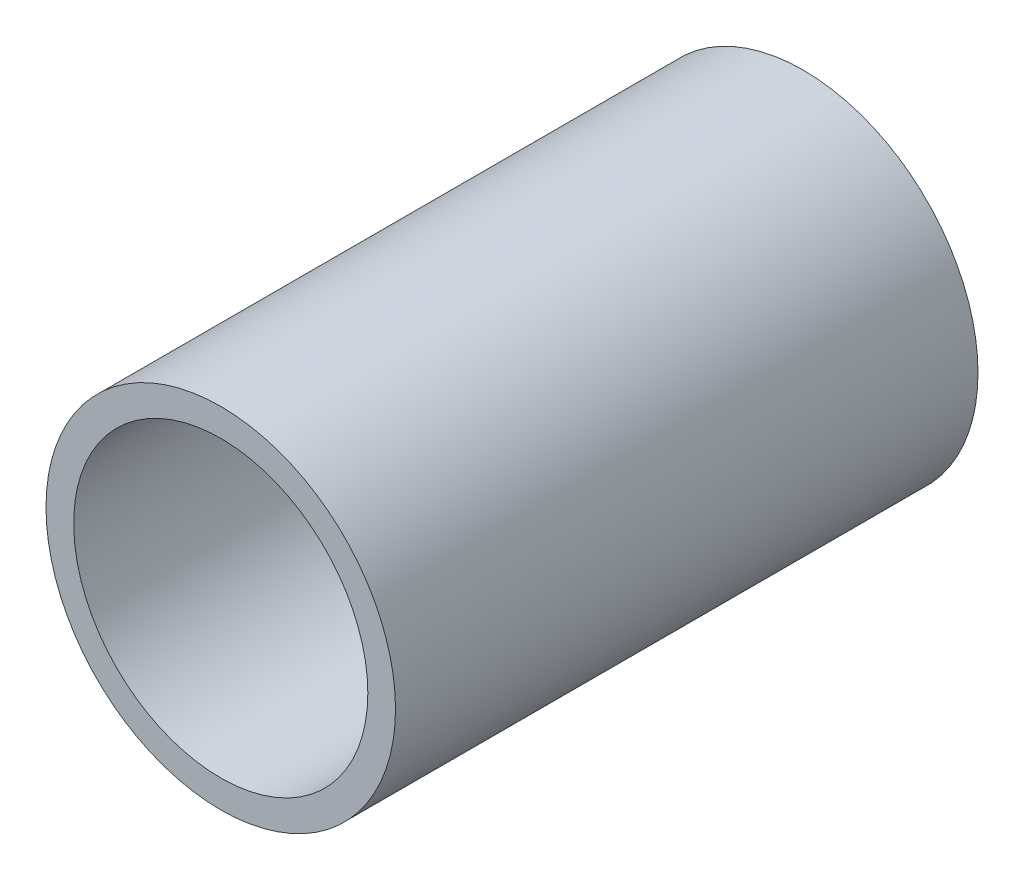
SolidWorks part; units mm, degrees
ref_plane "Front Plane" through (0, 0, 0) normal (0, 0, 1) x (1, 0, 0)
ref_plane "Top Plane" through (0, 0, 0) normal (0, 1, 0) x (1, 0, 0)
ref_plane "Right Plane" through (0, 0, 0) normal (1, 0, 0) x (0, 0, -1)
sketch "Sketch1" plane through (0, 0, 0) normal (0, 0, 1) x (1, 0, 0)
  circle A0 centre (0, 0) radius 9.525
  dimension "D1" = 19.05
extrude "Boss-Extrude1" add sketch "Sketch1" along normal blind 31.75 contours A0
hole_wizard "17/32 (0.53125) Diameter Hole3" positions "Sketch9" profile "Sketch10" hole size "17/32" standard "ANSI Inch"
sketch "Sketch9" plane through (0, 0, 31.75) normal (0, 0, 1) x (1, 0, 0)
  point P0 (0, 0)
sketch "Sketch10" plane through (0, 0, 31.75) normal (1, 0, 0) x (0, -1, 0)
  line L0 (0, 0) -> (0, 30.217)
  line L1 (0, 30.217) -> (8.0169, 25.4)
  line L2 (8.0169, 25.4) -> (8.0169, 0)
  line L5 (8.0169, 0) -> (0, 0)
  line L10 (0, 30.217) -> (-8.0169, 25.4) construction
  line L11 (0, -6.35) -> (0, 107.95) construction
  dimension "Hole Dia." = 16.0337
  dimension "Hole Depth" = 25.4
  dimension "Drill Angle" = 118
hole_wizard "CSK for 1/4 Flat Head Machine Screw (100)1" positions "Sketch11" profile "Sketch12" countersink size "1/4" standard "ANSI Inch"
sketch "Sketch11" plane through (0, 0, 0) normal (0, 0, -1) x (-1, 0, 0)
  point P0 (0, 0)
sketch "Sketch12" plane through (0, 0, 0) normal (1, 0, 0) x (0, 1, 0)
  line L0 (0, 0) -> (0, 27.4298)
  line L1 (0, 27.4298) -> (3.3782, 25.4)
  line L2 (3.3782, 25.4) -> (3.3782, 2.5682)
  line L3 (3.3782, 2.5682) -> (6.4389, 0)
  line L5 (6.4389, 0) -> (0, 0)
  line L6 (-3.3782, 2.5682) -> (-6.4389, 0) construction
  line L10 (0, 27.4298) -> (-3.3782, 25.4) construction
  line L11 (0, -6.35) -> (0, 107.95) construction
  dimension "Hole Dia." = 6.7564
  dimension "Hole Depth" = 25.4
  dimension "Near C'Sink Dia." = 12.8778
  dimension "Near C'Sink Angle" = 100
  dimension "Drill Angle" = 118
